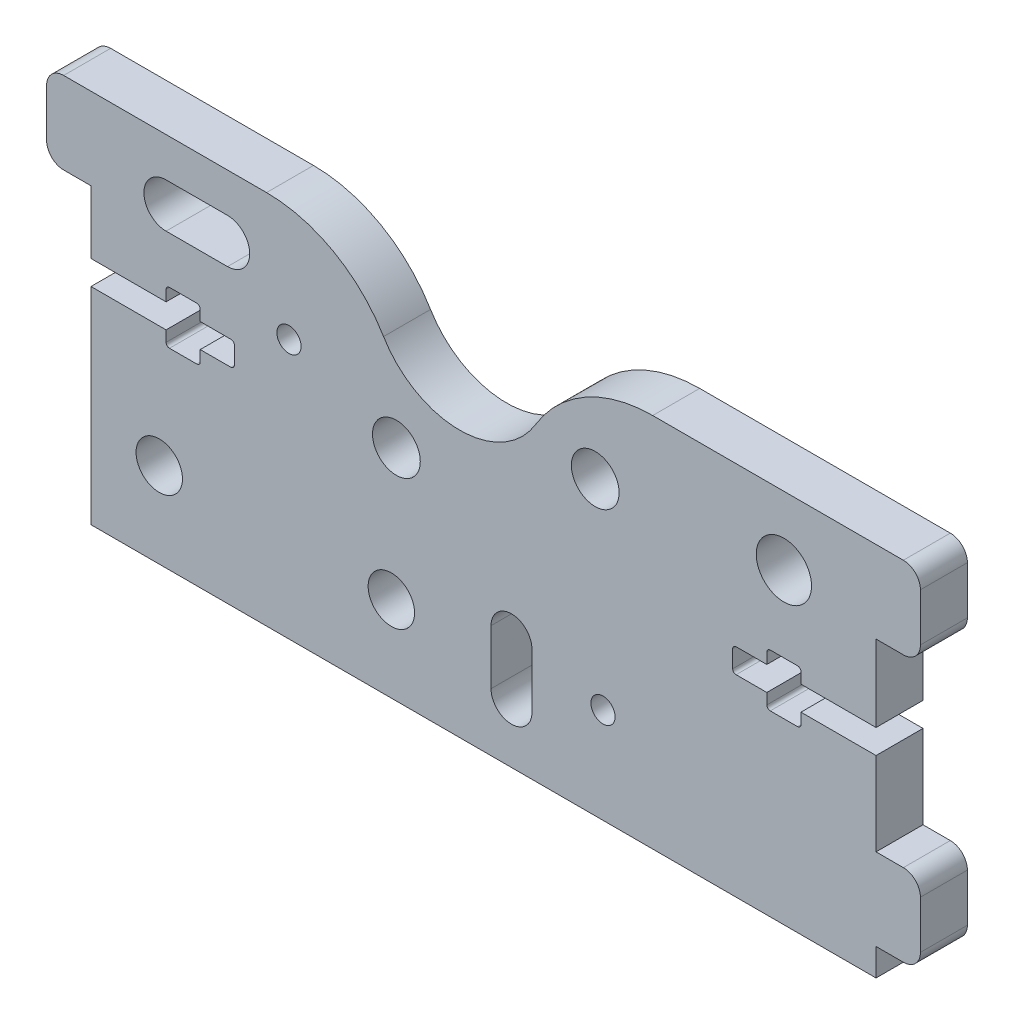
SolidWorks part; units mm, degrees
material "Melamine resin"
ref_plane "Front Plane" through (0, 0, 0) normal (0, 0, 1) x (1, 0, 0)
ref_plane "Top Plane" through (0, 0, 0) normal (0, 1, 0) x (1, 0, 0)
ref_plane "Right Plane" through (0, 0, 0) normal (1, 0, 0) x (0, 0, -1)
sketch "Sketch1" plane through (0, 0, 0) normal (0, 0, 1) x (1, 0, 0)
  line L1 (57.5, 27.5) -> (-57.5, 27.5)
  line L2 (57.5, 27.5) -> (57.5, -27.5)
  line L3 (57.5, -27.5) -> (-57.5, -27.5)
  line L4 (-57.5, 27.5) -> (-57.5, -27.5)
  line L5 (57.5, 27.5) -> (-57.5, -27.5) construction
  line L6 (57.5, -27.5) -> (-57.5, 27.5) construction
  line L7 (48, 20) -> (17, 20) construction
  line L8 (48, 20) -> (48, -11) construction
  line L9 (48, -11) -> (17, -11) construction
  line L10 (17, 20) -> (17, -11) construction
  line L11 (48, 20) -> (17, -11) construction
  line L12 (48, -11) -> (17, 20) construction
  circle A0 centre (17, 20) radius 3.5 construction
  circle A1 centre (32.5, 4.5) radius 13 construction
  circle A2 centre (48, 20) radius 3.5 construction
  circle A3 centre (48, -11) radius 3.5 construction
  circle A4 centre (17, -11) radius 3.5 construction
  point P0 (0, 0)
  point P5 (32.5, 4.5)
  dimension "D1" = 31
  dimension "D2" = 7
  dimension "D3" = 26
  dimension "D7" = 23
  dimension "D4" = 115
  dimension "D5" = 55
  dimension "D6" = 25
extrude "Boss-Extrude1" add sketch "Sketch1" along normal blind 6.88
sketch "Sketch2" plane through (0, 0, 6.88) normal (0, 0, 1) x (1, 0, 0)
  line L0 (-47.5, -15) -> (-13.5, -15) construction
  line L1 (-57.5, -27.5) -> (57.5, -27.5) construction
  line L2 (-57.5, 27.5) -> (-57.5, -27.5) construction
  circle A0 centre (-47.5, -15) radius 3.4
  circle A1 centre (-13.5, -15) radius 3.4
  dimension "D1" = 6.8
  dimension "D4" = 10
  dimension "D2" = 12.5
  dimension "D3" = 34
extrude "Cut-Extrude1" cut sketch "Sketch2" against normal through all
sketch "Sketch4" plane through (0, 0, 6.88) normal (0, 0, 1) x (1, 0, 0)
  line L0 (-47.5, -15) -> (-66.0382, -15) construction
  line L1 (-66.0382, 2.9858) -> (-22.2006, 2.9858) construction
  circle A0 centre (17.5, -13.5) radius 1.775
  circle A1 centre (17.5, -13.5) radius 12.7 construction
  circle A3 centre (-28.5, 10.5) radius 1.775
  circle A4 centre (-13.5, -15) radius 3.4 construction
  dimension "D1" = 3.55
  dimension "D2" = 25.4
  dimension "D4" = 24
  dimension "D6" = 1.5
  dimension "D3" = 31
  dimension "D5" = 46
extrude "Cut-Extrude3" cut sketch "Sketch4" against normal through all
sketch "Sketch6" plane through (0, 0, 6.88) normal (0, 0, 1) x (1, 0, 0)
  line L0 (57.5, -27.5) -> (57.5, 27.5) construction
  line L1 (51, 15.5) -> (64, 15.5)
  line L2 (51, 15.5) -> (51, 27.5)
  line L3 (51, 27.5) -> (64, 27.5)
  line L4 (64, 15.5) -> (64, 27.5)
  line L5 (51, 15.5) -> (64, 27.5) construction
  line L6 (51, 27.5) -> (64, 15.5) construction
  line L7 (-57.5, -27.5) -> (57.5, -27.5) construction
  line L8 (57.5, 27.5) -> (-57.5, 27.5) construction
  line L9 (45, -23.5) -> (64, -23.5)
  line L10 (45, -23.5) -> (45, -11.5)
  line L11 (45, -11.5) -> (64, -11.5)
  line L12 (64, -23.5) -> (64, -11.5)
  point P0 (57.5, 21.5)
  dimension "D1" = 6.5
  dimension "D2" = 12
  dimension "D4" = 12
  dimension "D5" = 4
extrude "Boss-Extrude2" add sketch "Sketch6" against normal up to surface (6.88 mm away) up to face at (-26.725, 10.5, 0)
sketch "Sketch7" plane through (0, 0, 6.88) normal (0, 0, 1) x (1, 0, 0)
  line L1 (78.5, 0.725) -> (36.5, 0.725)
  line L2 (78.5, 0.725) -> (78.5, 4.275)
  line L3 (78.5, 4.275) -> (36.5, 4.275)
  line L4 (36.5, 0.725) -> (36.5, 4.275)
  line L5 (78.5, 0.725) -> (36.5, 4.275) construction
  line L6 (78.5, 4.275) -> (36.5, 0.725) construction
  line L7 (57.5, -27.5) -> (57.5, -23.5) construction
  line L8 (-57.5, -27.5) -> (57.5, -27.5) construction
  line L9 (57.5, -11.5) -> (57.5, 15.5) construction
  point P0 (57.5, 2.5)
  dimension "D1" = 3.55
  dimension "D2" = 21
  dimension "D3" = 30
extrude "Cut-Extrude4" cut sketch "Sketch7" against normal through all
sketch "Sketch8" plane through (0, 0, 6.88) normal (0, 0, 1) x (1, 0, 0)
  line L0 (36.5, 2.5) -> (44, 2.5) construction
  line L1 (36.5, 4.275) -> (36.5, 0.725) construction
  line L2 (57.5, -27.5) -> (57.5, -23.5) construction
  line L3 (41.5, -1.36) -> (46.5, -1.36)
  line L4 (41.5, -1.36) -> (41.5, 6.36)
  line L5 (41.5, 6.36) -> (46.5, 6.36)
  line L6 (46.5, -1.36) -> (46.5, 6.36)
  line L7 (41.5, -1.36) -> (46.5, 6.36) construction
  line L8 (41.5, 6.36) -> (46.5, -1.36) construction
  dimension "D1" = 5
  dimension "D2" = 7.72
  dimension "D3" = 11
extrude "Cut-Extrude5" cut sketch "Sketch8" against normal through all
sketch "Sketch10" plane through (0, 0, 6.88) normal (0, 0, 1) x (1, 0, 0)
  line L0 (-57.5, -27.5) -> (57.5, -27.5) construction
  line L2 (-57.5, 27.5) -> (-57.5, -27.5) construction
  line L8 (-78.5, 6.275) -> (-36.5, 6.275)
  line L9 (-78.5, 6.275) -> (-78.5, 2.725)
  line L10 (-78.5, 2.725) -> (-36.5, 2.725)
  line L11 (-36.5, 6.275) -> (-36.5, 2.725)
  line L12 (-78.5, 6.275) -> (-36.5, 2.725) construction
  line L13 (-78.5, 2.725) -> (-36.5, 6.275) construction
  point P7 (-57.5, 4.5)
  dimension "D1" = 3.55
  dimension "D2" = 21
  dimension "D3" = 32
extrude "Cut-Extrude7" cut sketch "Sketch10" against normal through all
sketch "Sketch11" plane through (0, 0, 6.88) normal (0, 0, 1) x (1, 0, 0)
  line L0 (-57.5, 4.5) -> (-44, 4.5) construction
  line L1 (-57.5, 27.5) -> (-57.5, 6.275) construction
  line L2 (-46.5, 8.36) -> (-41.5, 8.36)
  line L3 (-46.5, 8.36) -> (-46.5, 0.64)
  line L4 (-46.5, 0.64) -> (-41.5, 0.64)
  line L5 (-41.5, 8.36) -> (-41.5, 0.64)
  line L6 (-46.5, 8.36) -> (-41.5, 0.64) construction
  line L7 (-46.5, 0.64) -> (-41.5, 8.36) construction
  dimension "D1" = 7.72
  dimension "D2" = 5
  dimension "D3" = 11
extrude "Cut-Extrude8" cut sketch "Sketch11" against normal through all
fillet "Fillet1" radius 0.5 12 edges at (36.5, 0.725, 3.44) (41.5, -1.36, 3.44) (36.5, 4.275, 3.44) (41.5, 6.36, 3.44) (46.5, -1.36, 3.44) (46.5, 6.36, 3.44) (-41.5, 8.36, 3.44) (-41.5, 0.64, 3.44) (-36.5, 2.725, 3.44) (-46.5, 0.64, 3.44) (-46.5, 8.36, 3.44) (-36.5, 6.275, 3.44)
sketch "Sketch13" plane through (0, 0, 6.88) normal (0, 0, 1) x (1, 0, 0)
  line L0 (4.1, -11) -> (4.1, -19) construction
  line L1 (7.1, -11) -> (7.1, -19)
  line L2 (1.1, -11) -> (1.1, -19)
  line L3 (-13.5, -15) -> (4.1, -15) construction
  arc A0 (7.1, -11) -> (1.1, -11) centre (4.1, -11) ccw
  arc A1 (1.1, -19) -> (7.1, -19) centre (4.1, -19) ccw
  point P2 (4.1, -15)
  dimension "D1" = 6
  dimension "D2" = 8
  dimension "D3" = 17.6
extrude "Cut-Extrude10" cut sketch "Sketch13" against normal through all
sketch "Sketch14" plane through (0, 0, 6.88) normal (0, 0, 1) x (1, 0, 0)
  line L1 (-57.5, 27.5) -> (-64, 27.5)
  line L2 (-57.5, 27.5) -> (-57.5, 15.5)
  line L3 (-57.5, 15.5) -> (-64, 15.5)
  line L4 (-64, 27.5) -> (-64, 15.5)
  dimension "D1" = 6.5
  dimension "D2" = 12
extrude "Boss-Extrude3" add sketch "Sketch14" against normal up to surface (6.88 mm away) up to face at (4.1, -15, 0)
sketch "Sketch15" plane through (0, 0, 6.88) normal (0, 0, 1) x (1, 0, 0)
  line L1 (-57.5, -27.5) -> (57.5, -27.5) construction
  circle A0 centre (-3.5, 24.5) radius 13
  circle A1 centre (-28.5, 10.5) radius 1.775 construction
  dimension "D2" = 52
  dimension "D3" = 26
  dimension "D1" = 25
extrude "Cut-Extrude11" cut sketch "Sketch15" against normal through all
fillet "Fillet2" radius 20 1 edges at (-16.1491, 27.5, 3.44)
sketch "Sketch17" plane through (0, 0, 6.88) normal (0, 0, 1) x (1, 0, 0)
  line L0 (57.5, 4.275) -> (57.5, 15.5) construction
  line L1 (64, 27.5) -> (24.7843, 27.5) construction
  line L2 (-46.5, 18.5) -> (-37.5, 18.5) construction
  line L3 (-46.5, 21.75) -> (-37.5, 21.75)
  line L4 (-46.5, 15.25) -> (-37.5, 15.25)
  line L5 (-31.7843, 27.5) -> (-64, 27.5) construction
  line L6 (-57.5, 15.5) -> (-57.5, 6.275) construction
  arc A0 (-46.5, 21.75) -> (-46.5, 15.25) centre (-46.5, 18.5) ccw
  arc A1 (-37.5, 15.25) -> (-37.5, 21.75) centre (-37.5, 18.5) ccw
  circle A2 centre (44, 17.5) radius 4.05
  point P2 (-42, 18.5)
  point P11 (44.3921, 27.5)
  dimension "D1" = 6.5
  dimension "D2" = 9
  dimension "D3" = 8.1
  dimension "D4" = 13.5
  dimension "D5" = 10
  dimension "D6" = 9
  dimension "D7" = 11
extrude "Cut-Extrude12" cut sketch "Sketch17" against normal through all
fillet "Fillet3" radius 2.5 6 edges at (64, 27.5, 3.44) (64, 15.5, 3.44) (64, -11.5, 3.44) (64, -23.5, 3.44) (-64, 15.5, 3.44) (-64, 27.5, 3.44)
sketch "Sketch18" plane through (0, 0, 6.88) normal (0, 0, 1) x (1, 0, 0)
  line L0 (-31.7843, 27.5) -> (-61.5, 27.5) construction
  line L1 (-23.3665, 33.7639) -> (5.7639, 44.3665) construction
  line L2 (-23.3665, 33.7639) -> (-12.7639, 4.6335) construction
  line L3 (-12.7639, 4.6335) -> (16.3665, 15.2361) construction
  line L4 (5.7639, 44.3665) -> (16.3665, 15.2361) construction
  line L5 (-23.3665, 33.7639) -> (16.3665, 15.2361) construction
  line L6 (-12.7639, 4.6335) -> (5.7639, 44.3665) construction
  circle A0 centre (-12.7639, 4.6335) radius 3.5
  circle A1 centre (16.3665, 15.2361) radius 3.5
  point P0 (-3.5, 24.5)
  dimension "D3" = 7
  dimension "D1" = 31
  dimension "D2" = 20
extrude "Cut-Extrude13" cut sketch "Sketch18" against normal through all
sketch "Sketch20" plane through (0, 0, 6.88) normal (0, 0, 1) x (1, 0, 0)
  text T0 "SeeMeCNC\r\n87908  R1" font "1CamBam_Stick_9" height 3
equation "\"22.1000mm..05\"=22.1"
